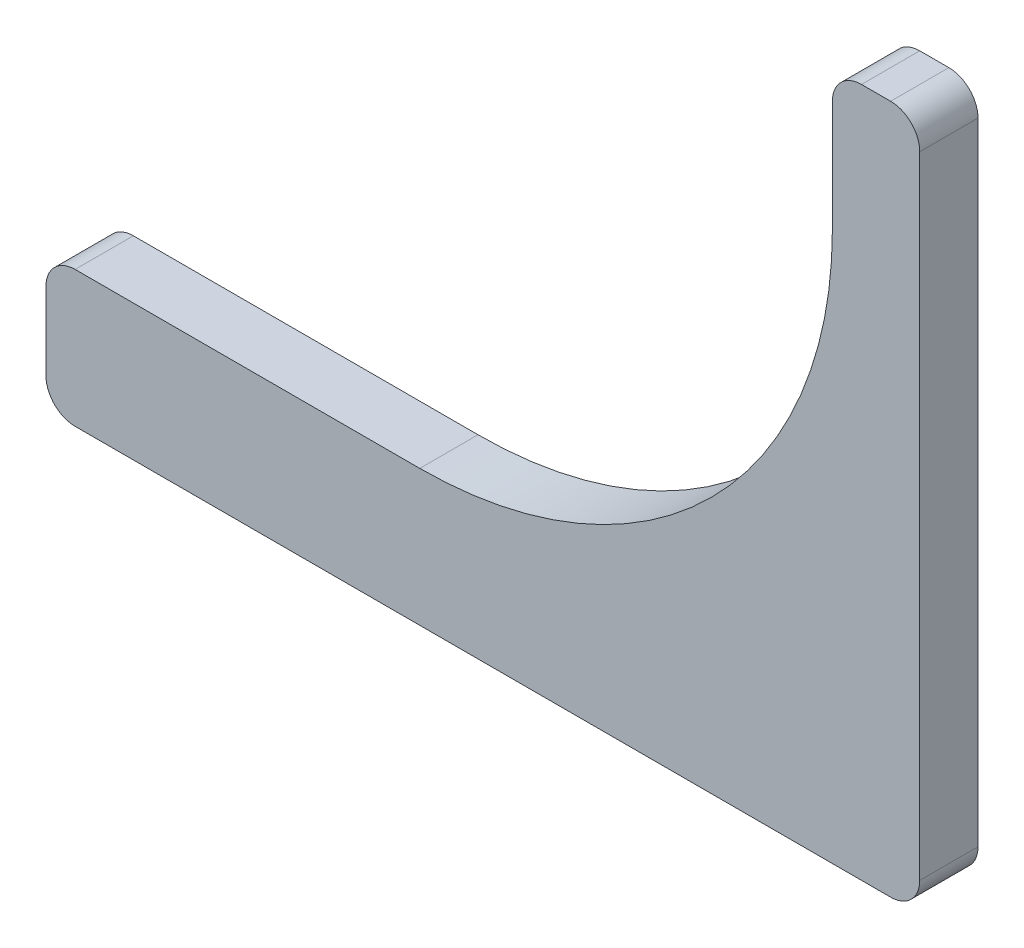
SolidWorks part; units mm, degrees
ref_plane "Plane1" through (0, 0, 0) normal (0, 0, 1) x (1, 0, 0)
ref_plane "Plane2" through (0, 0, 0) normal (0, 1, 0) x (1, 0, 0)
ref_plane "Plane3" through (0, 0, 0) normal (1, 0, 0) x (0, 0, -1)
sketch "Sketch1" plane through (0, 0, 0) normal (0, 0, 1) x (1, 0, 0)
  line L0 (-35.5, -56.5) -> (48.5, -56.5)
  line L1 (51.5, -53.5) -> (51.5, 11.5)
  line L2 (48.5, 14.5) -> (45.5, 14.5)
  line L3 (42.5, 11.5) -> (42.5, 0)
  line L4 (0, -42.5) -> (-35.5, -42.5)
  line L5 (-38.5, -45.5) -> (-38.5, -53.5)
  arc A0 (42.5, 0) -> (0, -42.5) centre (0, 0) cw
  arc A1 (51.5, 11.5) -> (48.5, 14.5) centre (48.5, 11.5) ccw
  arc A2 (45.5, 14.5) -> (42.5, 11.5) centre (45.5, 11.5) ccw
  arc A3 (-35.5, -42.5) -> (-38.5, -45.5) centre (-35.5, -45.5) ccw
  arc A4 (-35.5, -56.5) -> (-38.5, -53.5) centre (-35.5, -53.5) cw
  arc A5 (48.5, -56.5) -> (51.5, -53.5) centre (48.5, -53.5) ccw
  dimension "D1" = 42.5
  dimension "D6" = 3
  dimension "D2" = 71
  dimension "D3" = 51.5
  dimension "D4" = 56.5
  dimension "D5" = 90
extrude "Extrude1" add sketch "Sketch1" along normal blind 6
